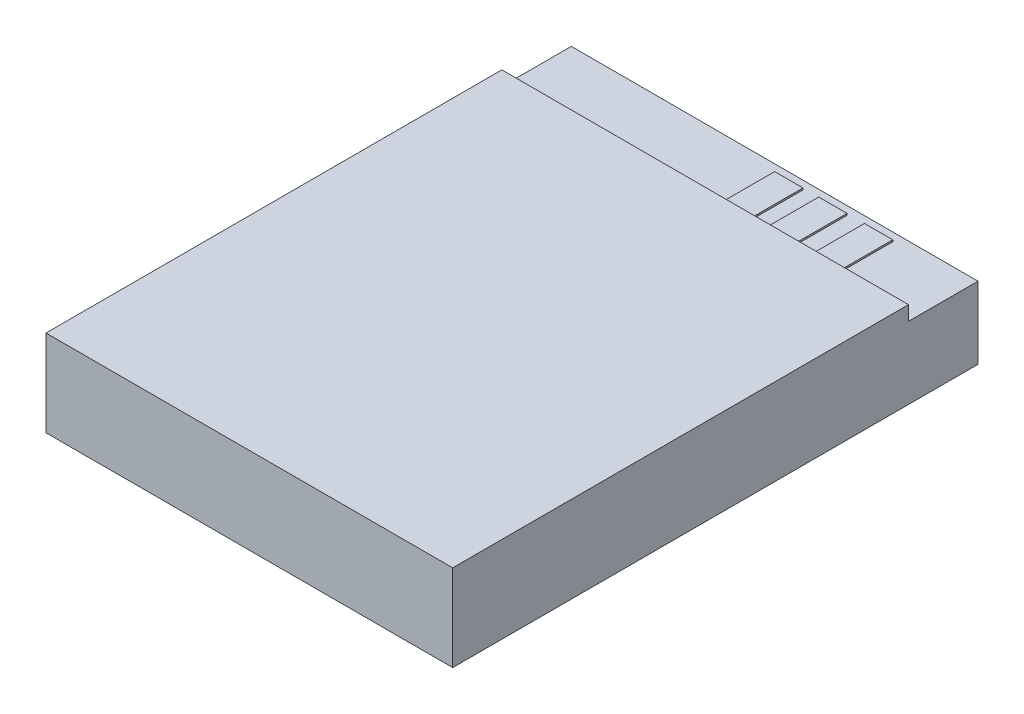
SolidWorks part; units mm, degrees
ref_plane "Спереди" through (0, 0, 0) normal (0, 0, 1) x (1, 0, 0)
ref_plane "Сверху" through (0, 0, 0) normal (0, 1, 0) x (1, 0, 0)
ref_plane "Справа" through (0, 0, 0) normal (1, 0, 0) x (0, 0, -1)
sketch "Эскиз1" plane through (0, 0, 0) normal (0, 1, 0) x (1, 0, 0)
  line L1 (-12, -15.5) -> (12, -15.5)
  line L2 (-12, -15.5) -> (-12, 15.5)
  line L3 (-12, 15.5) -> (12, 15.5)
  line L4 (12, -15.5) -> (12, 15.5)
  line L5 (-12, -15.5) -> (12, 15.5) construction
  line L6 (-12, 15.5) -> (12, -15.5) construction
  point P0 (0, 0)
  dimension "D1" = 31
  dimension "D2" = 24
extrude "Бобышка-Вытянуть1" add sketch "Эскиз1" along normal blind 5.1
sketch "Эскиз2" plane through (0, 5.1, 0) normal (0, 1, 0) x (1, 0, 0)
  line L0 (12, -15.5) -> (12, 15.5) construction
  line L1 (-12, 15.5) -> (12, 15.5)
  line L2 (-12, 15.5) -> (-12, 11.4)
  line L3 (-12, 11.4) -> (12, 11.4)
  line L4 (12, 15.5) -> (12, 11.4)
  dimension "D1" = 4.1
extrude "Вырез-Вытянуть1" cut sketch "Эскиз2" against normal blind 0.85 contours L3 L4 L1 L2
sketch "Эскиз3" plane through (0, 4.25, 0) normal (0, 1, 0) x (1, 0, 0)
  line L0 (12, 15.5) -> (12, 11.4) construction
  line L1 (0.5, 15) -> (2.17, 15)
  line L2 (0.5, 15) -> (0.5, 12)
  line L3 (0.5, 12) -> (2.17, 12)
  line L4 (2.17, 15) -> (2.17, 12)
  line L5 (3.1, 15) -> (4.77, 15)
  line L6 (3.1, 15) -> (3.1, 12)
  line L7 (3.1, 12) -> (4.77, 12)
  line L8 (4.77, 15) -> (4.77, 12)
  line L9 (5.8, 15) -> (7.47, 15)
  line L10 (5.8, 15) -> (5.8, 12)
  line L11 (5.8, 12) -> (7.47, 12)
  line L12 (7.47, 15) -> (7.47, 12)
  line L13 (-12, 15.5) -> (12, 15.5) construction
  dimension "D1" = 1.67
  dimension "D2" = 1.67
  dimension "D3" = 1.67
  dimension "D4" = 3
  dimension "D5" = 3
  dimension "D6" = 3
  dimension "D7" = 6.2
  dimension "D8" = 8.9
  dimension "D9" = 11.5
  dimension "D10" = 0.5
  dimension "D11" = 0.5
  dimension "D12" = 0.5
extrude "Бобышка-Вытянуть2" add sketch "Эскиз3" along normal blind 0.1
